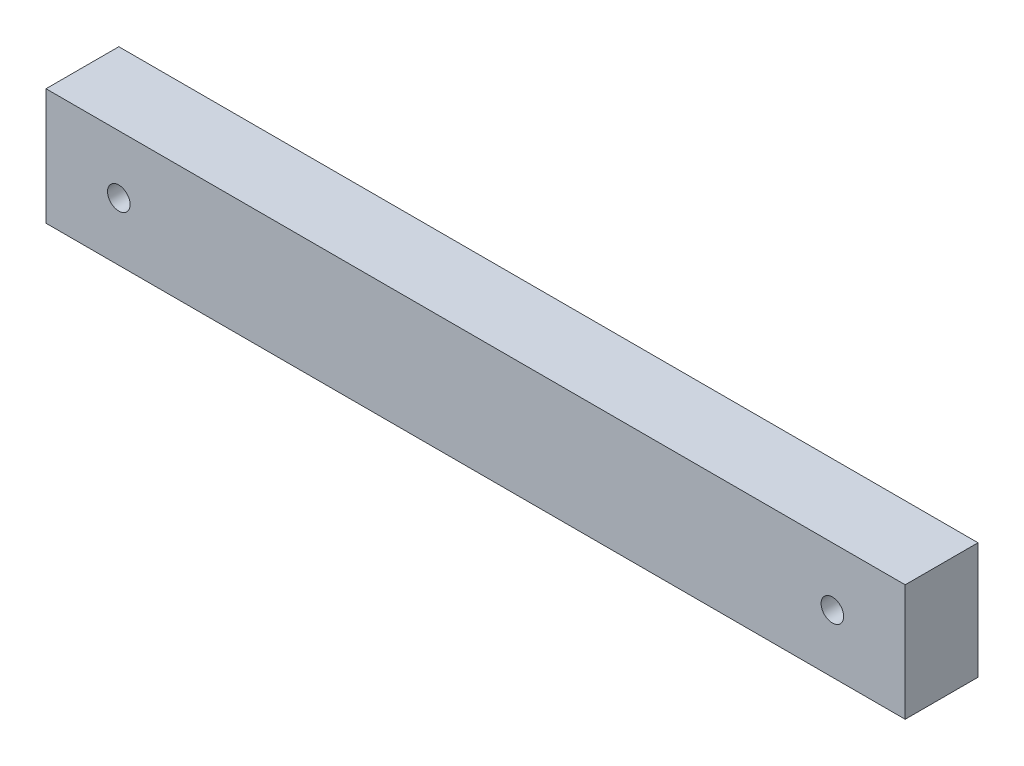
SolidWorks part; units mm, degrees
material "Carbon Sandwich"
ref_plane "Front Plane" through (0, 0, 0) normal (0, 0, 1) x (1, 0, 0)
ref_plane "Top Plane" through (0, 0, 0) normal (0, 1, 0) x (1, 0, 0)
ref_plane "Right Plane" through (0, 0, 0) normal (1, 0, 0) x (0, 0, -1)
sketch "Sketch1" plane through (0, 0, 0) normal (0, 0, 1) x (1, 0, 0)
  line L0 (0, 0) -> (50000, 0) construction
  line L1 (-59, -8) -> (59, -8)
  line L3 (-59, 8) -> (59, 8)
  line L5 (0, -8) -> (0, 8) construction
  line L6 (-59, 8) -> (-59, -8)
  line L8 (59, 8) -> (59, -8)
  circle A0 centre (-49, 0) radius 1.55
  circle A2 centre (49, 0) radius 1.55
  point P1 (-75, 0)
  point P3 (75, 0)
  dimension "D1" = 150
  dimension "D3" = 16
  dimension "D4" = 10
  dimension "D8" = 3.1
  dimension "D2" = 16
extrude "Boss-Extrude1" add sketch "Sketch1" along normal blind 10
